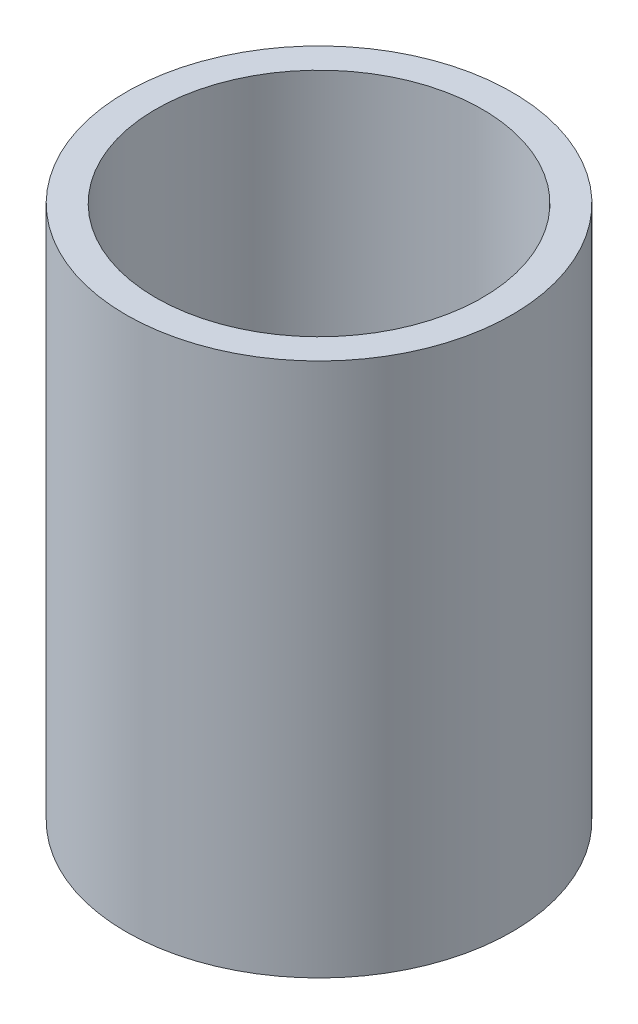
SolidWorks part; units mm, degrees
material "Nylon 101"
ref_plane "Front Plane" through (0, 0, 0) normal (0, 0, 1) x (1, 0, 0)
ref_plane "Top Plane" through (0, 0, 0) normal (0, 1, 0) x (1, 0, 0)
ref_plane "Right Plane" through (0, 0, 0) normal (1, 0, 0) x (0, 0, -1)
sketch "Sketch1" plane through (0, 0, 0) normal (0, 1, 0) x (1, 0, 0)
  circle A0 centre (0, 0) radius 3.25
  circle A1 centre (0, 0) radius 2.75
  dimension "D1" = 5.5
  dimension "D2" = 6.5
extrude "Boss-Extrude1" add sketch "Sketch1" along normal blind 9
